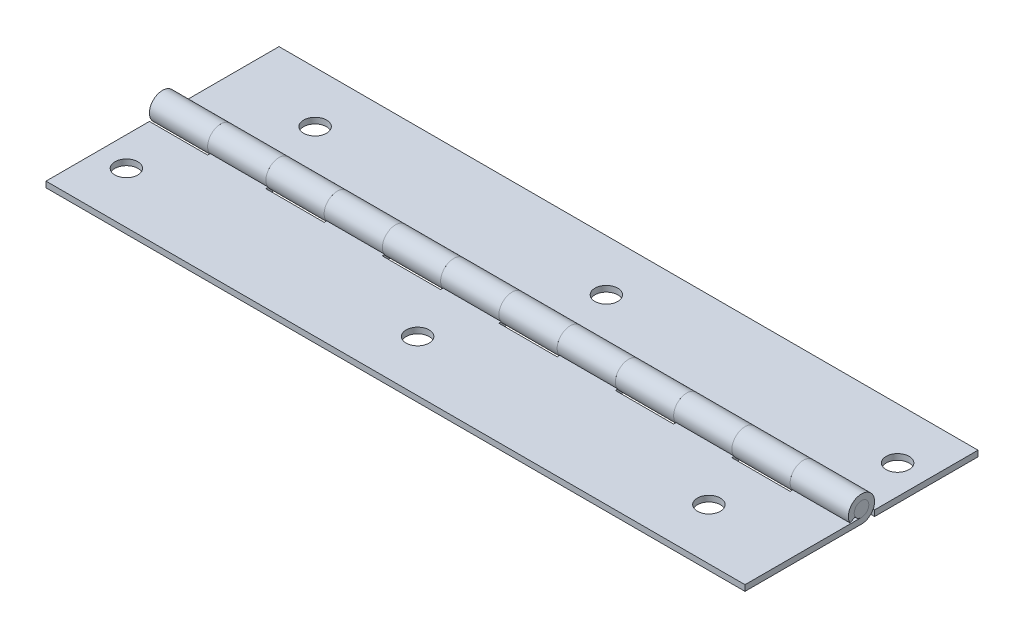
SolidWorks part; units mm, degrees
ref_plane "Front" through (0, 0, 0) normal (0, 0, 1) x (1, 0, 0)
ref_plane "Top" through (0, 0, 0) normal (0, 1, 0) x (1, 0, 0)
ref_plane "Right" through (0, 0, 0) normal (1, 0, 0) x (0, 0, -1)
sketch "Sketch1" plane through (0, 0, 0) normal (1, 0, 0) x (0, 0, -1)
  line L0 (-2.8575, -1.5875) -> (0, 0) construction
  line L1 (0, -1.5875) -> (-25.4, -1.5875)
  line L2 (-2.4979, -1.3877) -> (-1.3877, -0.771)
  line L3 (0, -2.8575) -> (-25.4, -2.8575)
  line L4 (-25.4, -1.5875) -> (-25.4, -2.8575)
  line L5 (-2.8575, 0) -> (-2.8575, -2.8575) construction
  line L6 (-25.4, -2.8575) -> (25.4, -2.8575) construction
  arc A0 (0, -1.5875) -> (-1.3877, -0.771) centre (0, 0) ccw
  arc A1 (0, -2.8575) -> (-2.4979, -1.3877) centre (0, 0) ccw
  dimension "Pin Dia" = 3.175
  dimension "Th" = 1.27
  dimension "Open Wd" = 50.8
extrude "Left Leaf" add sketch "Sketch1" along normal mid plane 152.4
sketch "Sketch2" plane through (0, 0, 0) normal (0, 1, 0) x (1, 0, 0)
  line L0 (76.2, 2.8575) -> (-76.2, 2.8575) construction
  line L2 (-50.8, 2.8575) -> (-38.1, 2.8575)
  line L3 (-50.8, 2.8575) -> (-50.8, -2.8575)
  line L4 (-50.8, -2.8575) -> (-38.1, -2.8575)
  line L5 (-38.1, 2.8575) -> (-38.1, -2.8575)
  line L9 (-76.2, -2.8575) -> (-63.5, -2.8575)
  line L10 (-76.2, -2.8575) -> (-76.2, 2.8575)
  line L11 (-76.2, 2.8575) -> (-63.5, 2.8575)
  line L12 (-63.5, -2.8575) -> (-63.5, 2.8575)
  line L13 (-76.2, -2.8575) -> (76.2, -2.8575) construction
  line L15 (50.8, 2.8575) -> (63.5, 2.8575)
  line L16 (50.8, 2.8575) -> (50.8, -2.8575)
  line L17 (50.8, -2.8575) -> (63.5, -2.8575)
  line L18 (-76.2, 0) -> (-76.2, -25.4) construction
  line L19 (63.5, 2.8575) -> (63.5, -2.8575)
  line L20 (-25.4, 2.8575) -> (-12.7, 2.8575)
  line L21 (-25.4, 2.8575) -> (-25.4, -2.8575)
  line L22 (-25.4, -2.8575) -> (-12.7, -2.8575)
  line L23 (-12.7, 2.8575) -> (-12.7, -2.8575)
  line L24 (0, 2.8575) -> (12.7, 2.8575)
  line L25 (0, 2.8575) -> (0, -2.8575)
  line L26 (0, -2.8575) -> (12.7, -2.8575)
  line L27 (12.7, 2.8575) -> (12.7, -2.8575)
  line L28 (25.4, 2.8575) -> (38.1, 2.8575)
  line L29 (25.4, 2.8575) -> (25.4, -2.8575)
  line L30 (25.4, -2.8575) -> (38.1, -2.8575)
  line L31 (38.1, 2.8575) -> (38.1, -2.8575)
  dimension "D1" = 12.7
  dimension "D2" = 12.7
  dimension "End Knuckle" = 12.7
  dimension "D3" = 12.7
  dimension "D4" = 12.7
  dimension "D5" = 12.7
extrude "Cut-Extrude1" cut sketch "Sketch2" against normal through all and the other way through all
sketch "Sketch3" plane through (0, 0, 0) normal (1, 0, 0) x (0, 0, -1)
  line L0 (0, 17.042) -> (0, -15.7543) construction
  line L1 (25.4, -1.5875) -> (25.4, -2.8575)
  line L2 (2.4979, -1.3877) -> (1.3877, -0.771)
  line L3 (0, -1.5875) -> (-25.4, -1.5875) construction
  line L8 (0, -2.8575) -> (-25.4, -2.8575) construction
  line L17 (25.4, -1.5875) -> (0, -1.5875)
  line L19 (0, -2.8575) -> (25.4, -2.8575)
  arc A0 (0, -2.8575) -> (-2.4979, -1.3877) centre (0, 0) ccw construction
  arc A1 (0, -1.5875) -> (-1.3877, -0.771) centre (0, 0) ccw construction
  arc A4 (2.4979, -1.3877) -> (0, -2.8575) centre (0, 0) ccw
  arc A5 (1.3877, -0.771) -> (0, -1.5875) centre (0, 0) ccw
extrude "Right Leaf" add sketch "Sketch3" along normal mid plane 152.4 separate body
sketch "Sketch9" plane through (0, 0, 0) normal (0, 1, 0) x (1, 0, 0)
  line L1 (-63.5, 2.8575) -> (-50.8, 2.8575)
  line L2 (-63.5, 2.8575) -> (-63.5, -2.8575)
  line L3 (-63.5, -2.8575) -> (-50.8, -2.8575)
  line L4 (-50.8, 2.8575) -> (-50.8, -2.8575)
  line L5 (-38.1, 2.8575) -> (-25.4, 2.8575)
  line L6 (-38.1, 2.8575) -> (-38.1, -2.8575)
  line L7 (-38.1, -2.8575) -> (-25.4, -2.8575)
  line L8 (-25.4, 2.8575) -> (-25.4, -2.8575)
  line L9 (-12.7, 2.8575) -> (0, 2.8575)
  line L10 (-12.7, 2.8575) -> (-12.7, -2.8575)
  line L11 (-12.7, -2.8575) -> (0, -2.8575)
  line L12 (0, 2.8575) -> (0, -2.8575)
  line L13 (12.7, 2.8575) -> (25.4, 2.8575)
  line L14 (12.7, 2.8575) -> (12.7, -2.8575)
  line L15 (12.7, -2.8575) -> (25.4, -2.8575)
  line L16 (25.4, 2.8575) -> (25.4, -2.8575)
  line L17 (38.1, 2.8575) -> (50.8, 2.8575)
  line L18 (38.1, 2.8575) -> (38.1, -2.8575)
  line L19 (38.1, -2.8575) -> (50.8, -2.8575)
  line L20 (50.8, 2.8575) -> (50.8, -2.8575)
  line L21 (63.5, 2.8575) -> (76.2, 2.8575)
  line L22 (63.5, 2.8575) -> (63.5, -2.8575)
  line L23 (63.5, -2.8575) -> (76.2, -2.8575)
  line L24 (76.2, 2.8575) -> (76.2, -2.8575)
extrude "Cut-Extrude2" cut sketch "Sketch9" against normal through all and the other way through all
sketch "Sketch10" plane through (0, 0, 0) normal (1, 0, 0) x (0, 0, -1)
  circle A0 centre (0, 0) radius 1.5875
  arc A1 (0, -1.5875) -> (-1.3877, -0.771) centre (0, 0) ccw construction
extrude "Extrude1" add sketch "Sketch10" along normal mid plane 152.4 separate body
sketch "Sketch11" plane through (0, -1.5875, 0) normal (0, 1, 0) x (-1, 0, 0)
  line L0 (-76.2, 25.4) -> (76.2, 25.4) construction
  line L1 (-76.2, 0) -> (-76.2, 25.4) construction
  line L2 (-76.2, -25.4) -> (-76.2, -2.8575) construction
  line L3 (-76.2, -25.4) -> (76.2, -25.4) construction
  line L4 (76.2, 2.8575) -> (76.2, 25.4) construction
  line L5 (76.2, -25.4) -> (76.2, 0) construction
  circle A0 centre (-69.85, -14.224) radius 2.5019
  circle A1 centre (-57.15, 14.224) radius 2.5019
  circle A2 centre (-6.35, -14.224) radius 2.5019
  circle A3 centre (6.35, 14.224) radius 2.5019
  circle A4 centre (69.85, 14.224) radius 2.5019
  circle A5 centre (57.15, -14.224) radius 2.5019
  point P0 (69.85, 14.224)
  point P1 (57.15, -14.224)
  point P2 (6.35, 14.224)
  point P3 (-6.35, -14.224)
  point P4 (-57.15, 14.224)
  point P5 (-69.85, -14.224)
  dimension "D7" = 5.0038
  dimension "D1" = 63.5
  dimension "Hole1" = 11.176
  dimension "D2" = 19.05
  dimension "D3" = 11.176
  dimension "Hole2" = 6.35
  dimension "D4" = 6.35
  dimension "D5" = 63.5
  dimension "D6" = 19.05
extrude "Cut-Extrude3" cut sketch "Sketch11" against normal through all
equation "\"D3@Sketch11\" = \"Hole1@Sketch11\""
